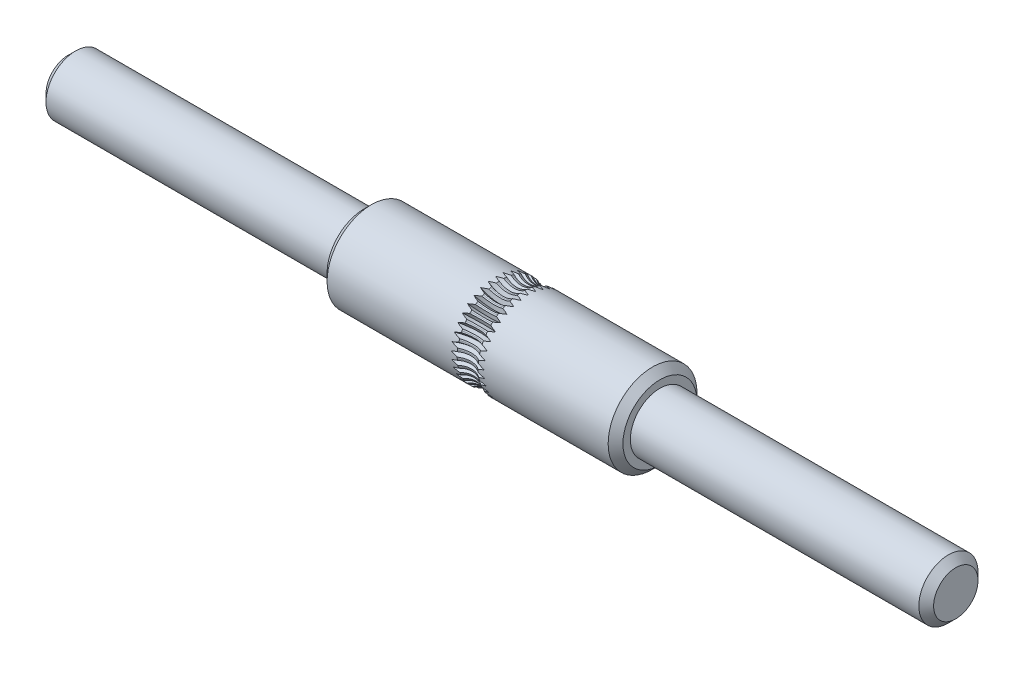
SolidWorks part; units mm, degrees
material "Plain Carbon Steel"
ref_plane "Front Plane" through (0, 0, 0) normal (0, 0, 1) x (1, 0, 0)
ref_plane "Top Plane" through (0, 0, 0) normal (0, 1, 0) x (1, 0, 0)
ref_plane "Right Plane" through (0, 0, 0) normal (1, 0, 0) x (0, 0, -1)
sketch "Sketch1" plane through (0, 0, 0) normal (0, 0, 1) x (1, 0, 0)
  line L0 (-10, 3) -> (10, 3)
  line L1 (-10, 3) -> (-10, 2)
  line L2 (-30, 0) -> (30, 0)
  line L3 (-30, 0) -> (-30, 2)
  line L4 (-30, 2) -> (-10, 2)
  line L5 (30, 0) -> (30, 2)
  line L6 (10, 3) -> (10, 2)
  line L7 (10, 2) -> (30, 2)
  line L8 (0, 0) -> (67.2135, 0) construction
  line L9 (0, 0) -> (0, 19.6593) construction
  dimension "D1" = 6
  dimension "D2" = 20
  dimension "D3" = 20
  dimension "D4" = 20
  dimension "D5" = 4
revolve "Revolve1" add sketch "Sketch1" angle 360 about L8
chamfer "Chamfer1" distance 0.5 angle 45 4 edges at (30, 0, 2) (10, 0, 3) (-10, 0, 3) (-30, 0, 2)
sketch "Sketch2" plane through (0, 0, 0) normal (1, 0, 0) x (0, 0, -1)
  line L0 (0, 0) -> (0, 4) construction
  line L1 (9.9899, 4) -> (-9.864, 4) construction
  line L2 (0.1562, 2.7705) -> (0, 2.5)
  line L3 (0, 2.5) -> (-0.1562, 2.7705)
  line L4 (-1.1508, 4) -> (1.1508, 4)
  line L5 (-0.1562, 2.7705) -> (-1.1508, 2.7705)
  line L6 (0.1562, 2.7705) -> (1.1508, 2.7705)
  line L7 (1.1508, 2.7705) -> (1.1508, 4)
  line L8 (-1.1508, 2.7705) -> (-1.1508, 4)
  line L9 (0, 0) -> (-6.9817, 0) construction
  line L10 (5.645, 3) -> (-5.97, 3) construction
  circle A0 centre (0, 0) radius 3 construction
  circle A1 centre (0, 0) radius 2.5 construction
  dimension "D1" = 60
  dimension "D2" = 3
  dimension "D3" = 2.459
  dimension "D4" = 1
revolve "Cut-Revolve1" cut sketch "Sketch2" angle 360 about L1
pattern_circular "CirPattern1" count 37 over 360 about axis through (0, 0, 0) along (-1, 0, 0) of "Cut-Revolve1"
sketch "Sketch3" plane through (0, 0, 0) normal (0, 0, 1) x (1, 0, 0)
  line L0 (29.5, 2) -> (10, 2) construction
  line L1 (8, 3) -> (0.75, 3)
  line L2 (8, 3) -> (8, 2)
  line L3 (8, 2) -> (0.75, 2)
  line L4 (0.75, 3) -> (0.75, 2)
  line L5 (-0.75, 3) -> (-8, 3)
  line L6 (-0.75, 3) -> (-0.75, 2)
  line L7 (-0.75, 2) -> (-8, 2)
  line L8 (-8, 3) -> (-8, 2)
  line L9 (0, 0) -> (0, 15.3026) construction
  line L10 (0, 0) -> (-13.7134, 0) construction
  line L11 (9.5, 3) -> (1.118, 3) construction
  dimension "D1" = 1.5
  dimension "D2" = 16
revolve "Cut-Revolve2" [suppressed] cut sketch "Sketch3" angle 360 about L10
